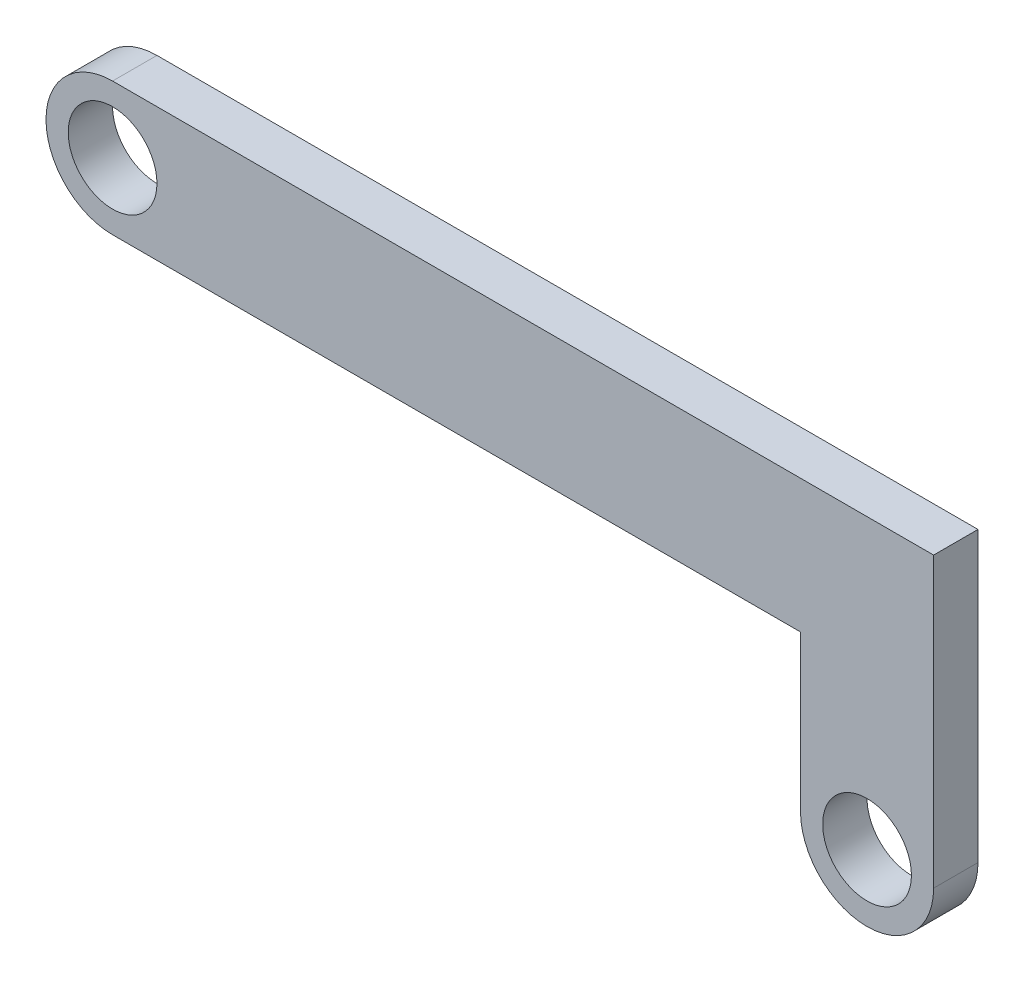
SolidWorks part; units mm, degrees
ref_plane "Front Plane" through (0, 0, 0) normal (0, 0, 1) x (1, 0, 0)
ref_plane "Top Plane" through (0, 0, 0) normal (0, 1, 0) x (1, 0, 0)
ref_plane "Right Plane" through (0, 0, 0) normal (1, 0, 0) x (0, 0, -1)
sketch "Sketch1" plane through (0, 0, 0) normal (0, 0, 1) x (1, 0, 0)
  line L0 (0, 36.0099) -> (0, -41.8046) construction
  line L1 (-71.9754, 0) -> (95.4087, 0) construction
  line L3 (-73.2833, -1.8046) -> (26.7167, -1.8046)
  line L4 (-73.2833, -1.8046) -> (-73.2833, -16.8046)
  line L5 (-73.2833, -16.8046) -> (11.7167, -16.8046)
  line L8 (11.7167, -16.8046) -> (11.7167, -41.8046)
  line L9 (11.7167, -41.8046) -> (26.7167, -41.8046)
  line L10 (26.7167, -1.8046) -> (26.7167, -41.8046)
  dimension "D1" = 100
  dimension "D2" = 15
  dimension "D3" = 15
  dimension "D4" = 40
extrude "Boss-Extrude1" add sketch "Sketch1" along normal blind 5
sketch "Sketch2" plane through (0, 0, 5) normal (0, 0, 1) x (1, 0, 0)
  line L0 (-73.2833, -9.3046) -> (26.7167, -9.3046) construction
  line L1 (-73.2833, -1.8046) -> (-73.2833, -16.8046) construction
  line L2 (26.7167, -41.8046) -> (26.7167, -1.8046) construction
  line L3 (19.2167, -41.8046) -> (19.2167, -0.7187) construction
  line L4 (11.7167, -41.8046) -> (26.7167, -41.8046) construction
  line L11 (-73.2833, -1.8046) -> (-73.2833, -16.8046)
  line L12 (-73.2833, -16.8046) -> (11.7167, -16.8046)
  line L13 (11.7167, -16.8046) -> (11.7167, -41.8046)
  line L14 (11.7167, -41.8046) -> (26.7167, -41.8046)
  line L15 (26.7167, -41.8046) -> (26.7167, -1.8046)
  line L16 (26.7167, -1.8046) -> (-73.2833, -1.8046)
  line L17 (-73.2833, -1.8046) -> (-73.2833, -16.8046)
  line L18 (-73.2833, -16.8046) -> (11.7167, -16.8046)
  line L19 (11.7167, -16.8046) -> (11.7167, -41.8046)
  line L20 (11.7167, -41.8046) -> (26.7167, -41.8046)
  line L21 (26.7167, -41.8046) -> (26.7167, -1.8046)
  line L22 (26.7167, -1.8046) -> (-73.2833, -1.8046)
  circle A0 centre (-65.7833, -9.3046) radius 7.5
  circle A1 centre (19.2167, -34.3046) radius 7.5
  circle A2 centre (-65.7833, -9.3046) radius 5
  circle A3 centre (19.2167, -34.3046) radius 5
  line M8 (-73.2833, -1.8046) -> (-73.2833, -16.8046)
  line M9 (-73.2833, -16.8046) -> (11.7167, -16.8046)
  line M11 (11.7167, -41.8046) -> (26.7167, -41.8046)
  line M12 (26.7167, -41.8046) -> (26.7167, -1.8046)
  dimension "D1" = 15
  dimension "D2" = 15
  dimension "D5" = 0
  dimension "D3" = 7.5
  dimension "D4" = 7.5
extrude "Cut-Extrude1" cut sketch "Sketch2" against normal blind 5 contours A3 | A1 L19 M11 | A1 L20 M12 | A2 | A0 L22 M8 | A0 L17 M9
